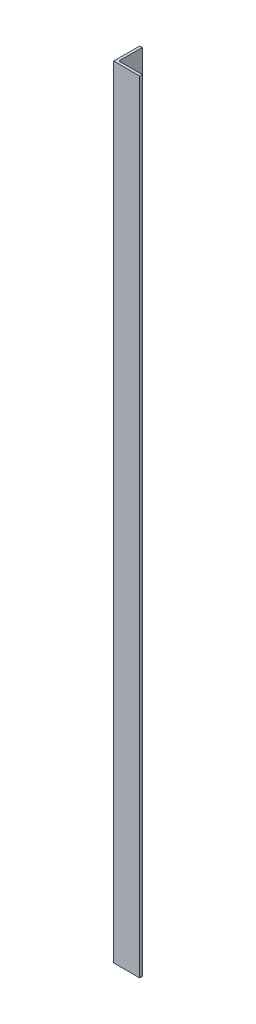
SolidWorks part; units mm, degrees
ref_plane "Спереди" through (0, 0, 0) normal (0, 0, 1) x (1, 0, 0)
ref_plane "Сверху" through (0, 0, 0) normal (0, 1, 0) x (1, 0, 0)
ref_plane "Справа" through (0, 0, 0) normal (1, 0, 0) x (0, 0, -1)
sketch "Эскиз1" plane through (0, 0, 0) normal (0, 1, 0) x (1, 0, 0)
  line L0 (0, 0) -> (0, 50)
  line L1 (0, 0) -> (50, 0)
extrude "Вытянуть-Тонкостенный1" add sketch "Эскиз1" along normal blind 1500 thin
